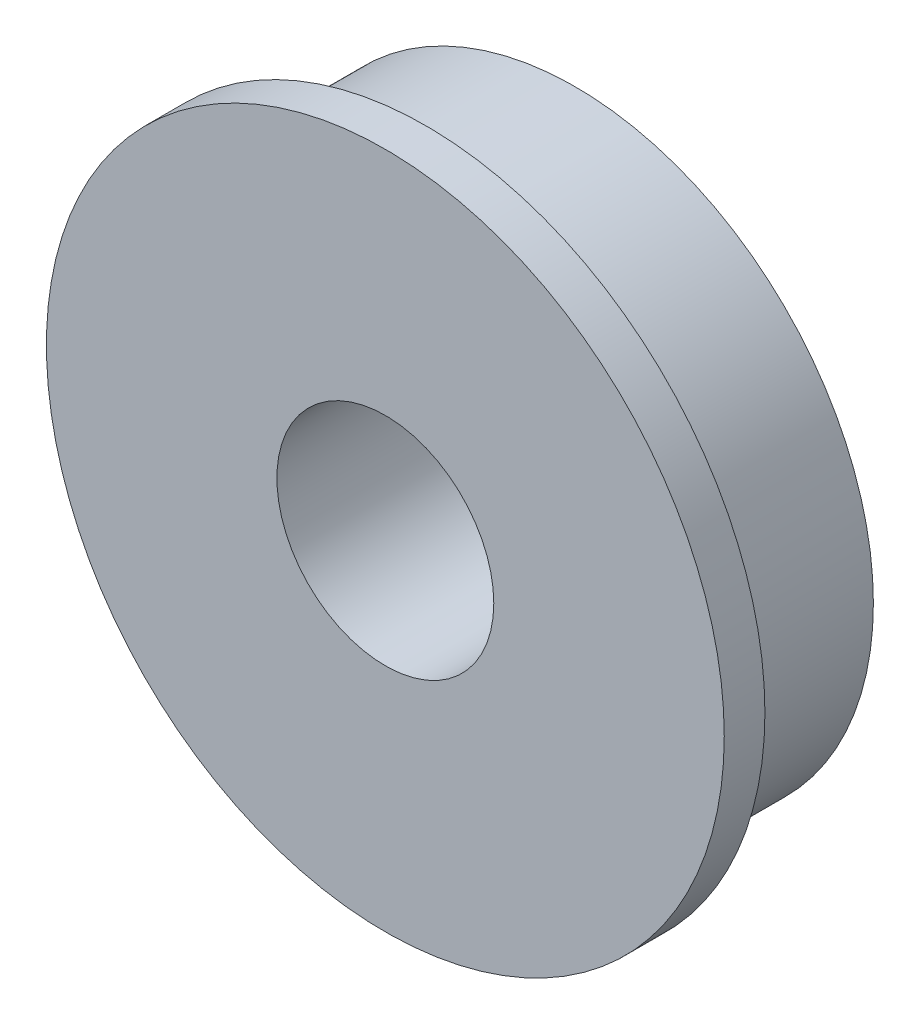
SolidWorks part; units mm, degrees
ref_plane "Plan de face" through (0, 0, 0) normal (0, 0, 1) x (1, 0, 0)
ref_plane "Plan de dessus" through (0, 0, 0) normal (0, 1, 0) x (1, 0, 0)
ref_plane "Plan de droite" through (0, 0, 0) normal (1, 0, 0) x (0, 0, -1)
sketch "Esquisse1" plane through (0, 0, 0) normal (0, 0, 1) x (1, 0, 0)
  circle A0 centre (0, 0) radius 11
  circle A1 centre (0, 0) radius 4
  dimension "D1" = 8
  dimension "D2" = 22
extrude "Boss.-Extru.1" add sketch "Esquisse1" along normal blind 5.5
sketch "Esquisse2" plane through (0, 0, 5.5) normal (0, 0, 1) x (1, 0, 0)
  circle A0 centre (0, 0) radius 4
  circle A1 centre (0, 0) radius 12.5
  dimension "D1" = 25
extrude "Boss.-Extru.2" add sketch "Esquisse2" along normal blind 1.5
